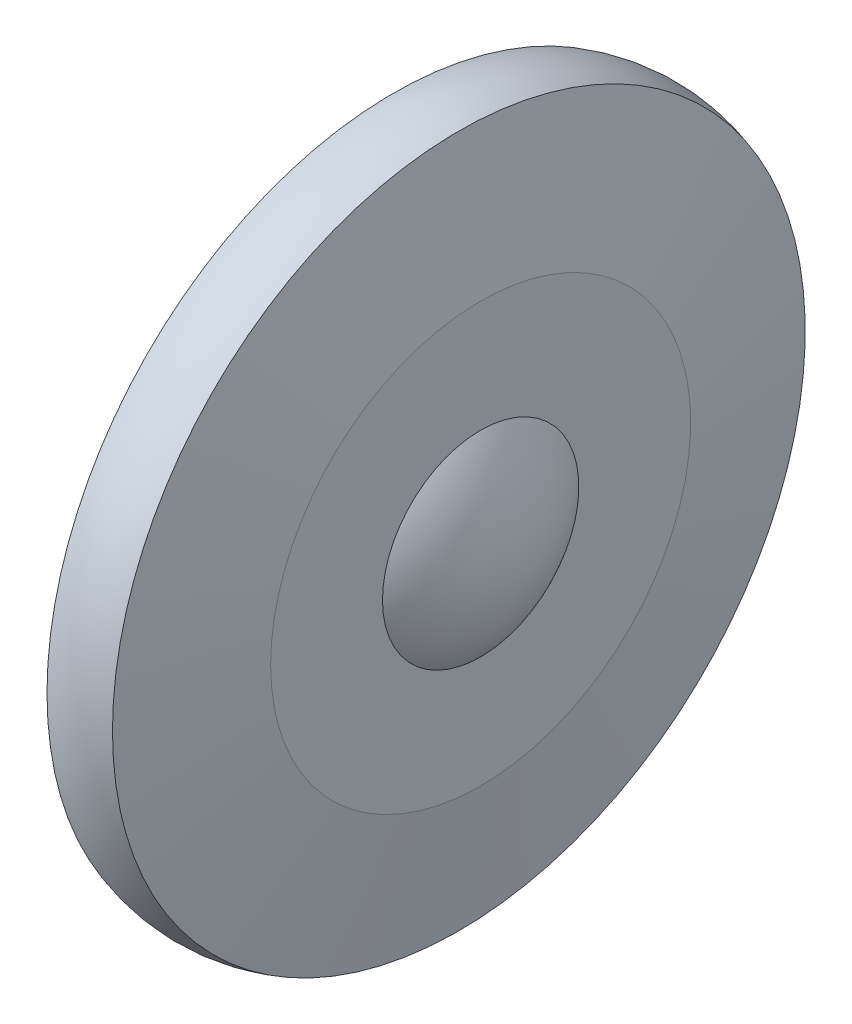
SolidWorks part; units mm, degrees
material "AISI 1020"
ref_plane "Спереди" through (0, 0, 0) normal (0, 0, 1) x (1, 0, 0)
ref_plane "Сверху" through (0, 0, 0) normal (0, 1, 0) x (1, 0, 0)
ref_plane "Справа" through (0, 0, 0) normal (1, 0, 0) x (0, 0, -1)
sketch "Эскиз1" plane through (0, 0, 0) normal (0, 0, 1) x (1, 0, 0)
  line L0 (-755.2351, 0) -> (37006.5213, 0) construction
  line L1 (0, -755.2351) -> (0, 37006.5213) construction
  line L2 (6, 18) -> (6, 23.5)
  line L3 (6, 23.5) -> (-8, 23.5)
  line L4 (-8, 23.5) -> (-8, 25.5)
  line L5 (-8, 25.5) -> (-9.7, 25.5)
  line L6 (-9.7, 25.5) -> (-9.7, 23.5)
  line L7 (-9.7, 23.5) -> (-19, 23.5)
  line L8 (-19, 23.5) -> (-19, 29.75)
  line L9 (-19, 29.75) -> (-10, 29.75)
  line L10 (-10, 29.75) -> (-10, 38.5)
  line L11 (-10, 38.5) -> (-6, 63.5)
  line L12 (-10, 38.5) -> (10, 38.5) construction
  line L13 (6, 63.5) -> (10, 38.5)
  line L14 (10, 38.5) -> (10, 18)
  line L15 (12.9072, 0) -> (16, 0)
  arc A0 (12.9072, 0) -> (6, 18) centre (-14, 0) ccw
  arc A1 (10, 18) -> (16, 0) centre (-14, 0) cw
  arc A2 (-6, 63.5) -> (6, 63.5) centre (0, 46) cw
  point P23 (0, 38.5)
  point P24 (6, 0)
  point P25 (0, 0)
  point P26 (6, 22.0663)
  point P28 (6, 18)
  point P29 (0, 0)
  dimension "D2" = 129
  dimension "D1" = 12
  dimension "D3" = 47
  dimension "D4" = 20
  dimension "D5" = 59.5
  dimension "D6" = 14
  dimension "D7" = 25
  dimension "D8" = 9
  dimension "D9" = 1.7
  dimension "D10" = 2
  dimension "D11" = 36
  dimension "D12" = 6
  dimension "D13" = 77
  dimension "D14" = 127
revolve "Повернуть1" add sketch "Эскиз1" angle 360 about L15
chamfer "Фаска1" distance 3 angle 45 1 edges at (-19, 0, 29.75)
